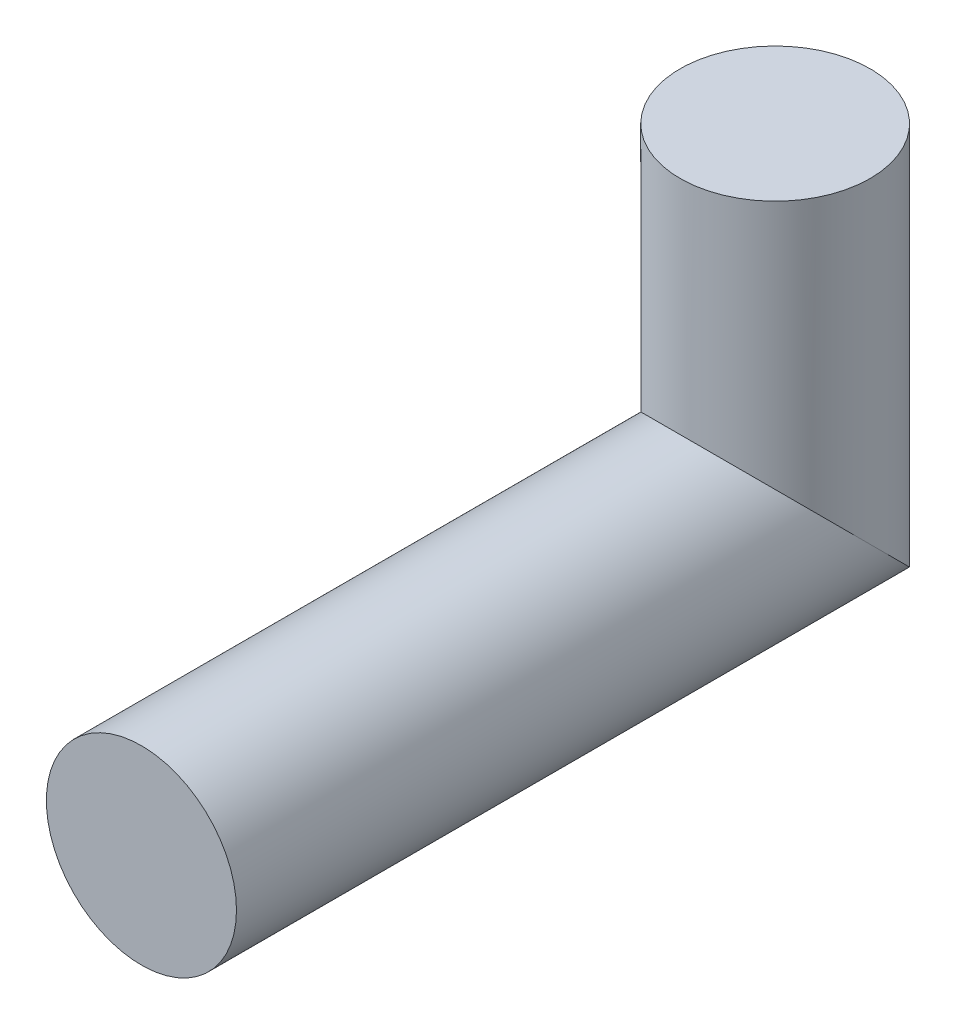
SolidWorks part; units mm, degrees
ref_plane "Front Plane" through (0, 0, 0) normal (0, 0, 1) x (1, 0, 0)
ref_plane "Top Plane" through (0, 0, 0) normal (0, 1, 0) x (1, 0, 0)
ref_plane "Right Plane" through (0, 0, 0) normal (1, 0, 0) x (0, 0, -1)
sketch "Sketch1" plane through (0, 0, 0) normal (0, 0, 1) x (1, 0, 0)
  circle A0 centre (0, 0) radius 19.05
  dimension "D1" = 38.1
sketch "Sketch2" plane through (0, 0, 0) normal (1, 0, 0) x (0, 0, -1)
  line L0 (0, 0) -> (127, 0)
  line L1 (127, 0) -> (127, 63.5)
  dimension "D1" = 63.5
  dimension "D2" = 127
sweep "Sweep1" add profiles "Sketch1" path "Sketch2"
ref_plane "turn_Plane" through (0, 0, -127) normal (0, 0, 1) x (1, 0, 0)
